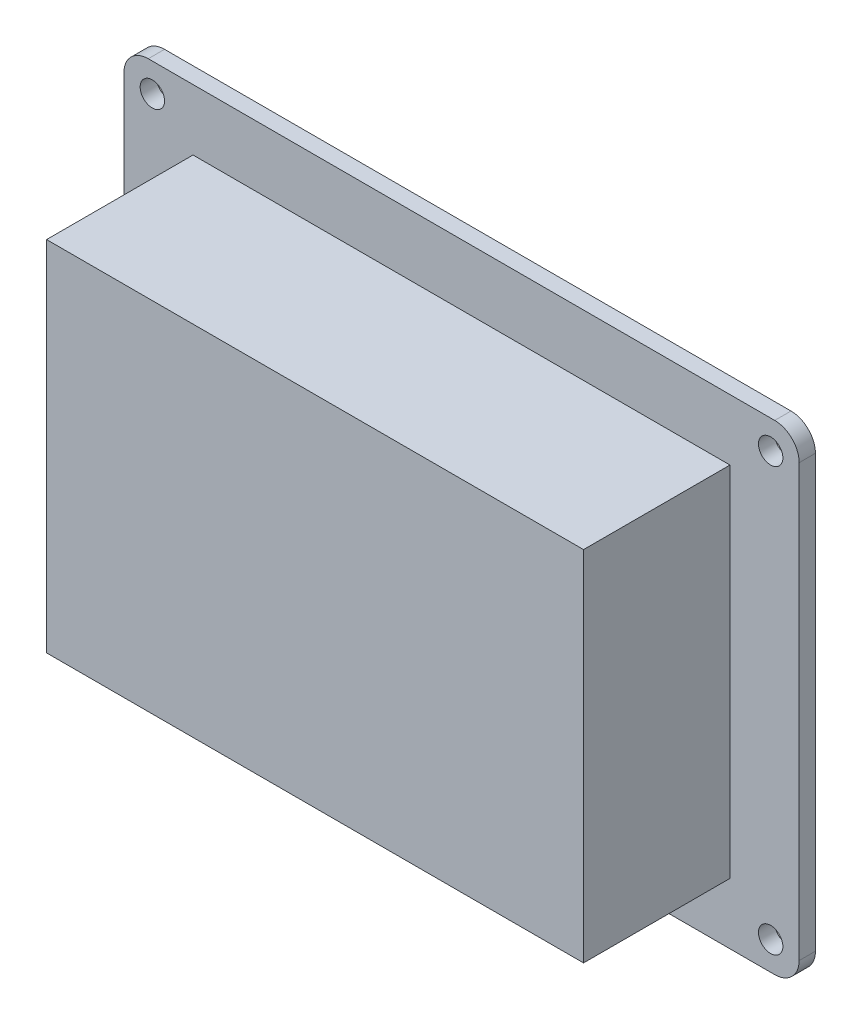
SolidWorks part; units mm, degrees
ref_plane "Front Plane" through (0, 0, 0) normal (0, 0, 1) x (1, 0, 0)
ref_plane "Top Plane" through (0, 0, 0) normal (0, 1, 0) x (1, 0, 0)
ref_plane "Right Plane" through (0, 0, 0) normal (1, 0, 0) x (0, 0, -1)
sketch "Sketch1" plane through (0, 0, 0) normal (0, 0, 1) x (1, 0, 0)
  line L1 (0, 0) -> (83, 0)
  line L2 (0, 0) -> (0, 59)
  line L3 (0, 59) -> (83, 59)
  line L4 (83, 0) -> (83, 59)
  dimension "D1" = 59
  dimension "D2" = 83
extrude "Boss-Extrude1" add sketch "Sketch1" along normal blind 2
fillet "Fillet1" radius 3 4 edges at (83, 59, 1) (83, 0, 1) (0, 0, 1) (0, 59, 1)
sketch "Sketch2" plane through (0, 0, 2) normal (0, 0, 1) x (1, 0, 0)
  line L0 (83, 3) -> (83, 56) construction
  line L1 (3.5, 55.5) -> (79.5, 55.5)
  line L2 (3.5, 55.5) -> (3.5, 3.5)
  line L3 (3.5, 3.5) -> (79.5, 3.5)
  line L4 (79.5, 55.5) -> (79.5, 3.5)
  line L5 (3, 0) -> (80, 0) construction
  circle A0 centre (3.5, 55.5) radius 1.5
  circle A1 centre (79.5, 55.5) radius 1.5
  dimension "D5" = 3
  dimension "D6" = 3
  dimension "D1" = 52
  dimension "D2" = 76
  dimension "D3" = 3.5
  dimension "D4" = 3.5
ref_plane "Plane1" through (0, 29.5, 0) normal (0, -1, 0) x (-1, 0, 0)
extrude "Cut-Extrude1" cut sketch "Sketch2" against normal up to next (2 mm away) contours A0 | A1
mirror "Mirror1" about plane through (0, 29.5, 0) normal (0, -1, 0) of "Cut-Extrude1"
sketch "Sketch4" plane through (0, 0, 2) normal (0, 0, 1) x (1, 0, 0)
  line L0 (-1.1, 29.5) -> (1.1, 29.5) construction
  line L1 (8.5, 51.5) -> (74.5, 51.5)
  line L2 (8.5, 51.5) -> (8.5, 7.5)
  line L3 (8.5, 7.5) -> (74.5, 7.5)
  line L4 (74.5, 51.5) -> (74.5, 7.5)
  line L5 (83, 3) -> (83, 56) construction
  dimension "D1" = 66
  dimension "D2" = 44
  dimension "D3" = 22
  dimension "D4" = 8.5
extrude "Boss-Extrude2" add sketch "Sketch4" along normal blind 18
